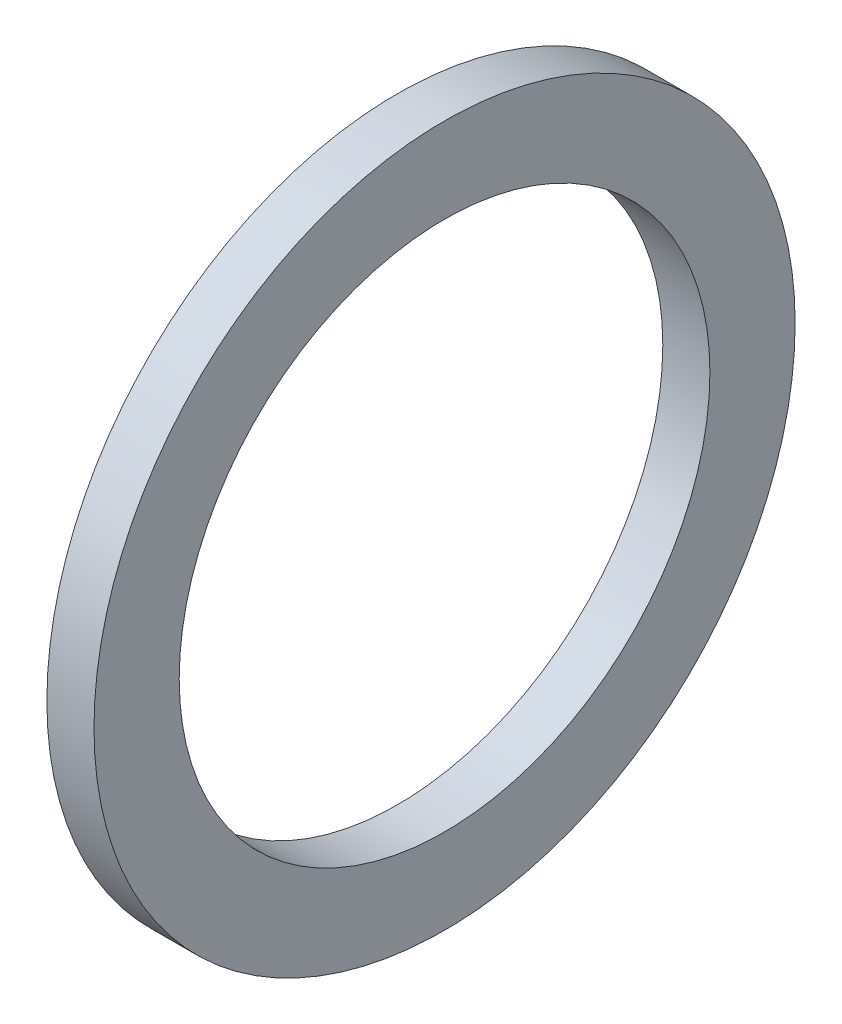
SolidWorks part; units mm, degrees
material "Nylon 101"
ref_plane "Front Plane" through (0, 0, 0) normal (0, 0, 1) x (1, 0, 0)
ref_plane "Top Plane" through (0, 0, 0) normal (0, 1, 0) x (1, 0, 0)
ref_plane "Right Plane" through (0, 0, 0) normal (1, 0, 0) x (0, 0, -1)
sketch "Sketch1" plane through (0, 0, 0) normal (1, 0, 0) x (0, 0, -1)
  circle A0 centre (0, 0) radius 4.8641
  circle A1 centre (0, 0) radius 6.4262
  dimension "OD" = 9.7282
  dimension "ID" = 12.8524
extrude "Boss-Extrude1" add sketch "Sketch1" along normal blind 0.8636
